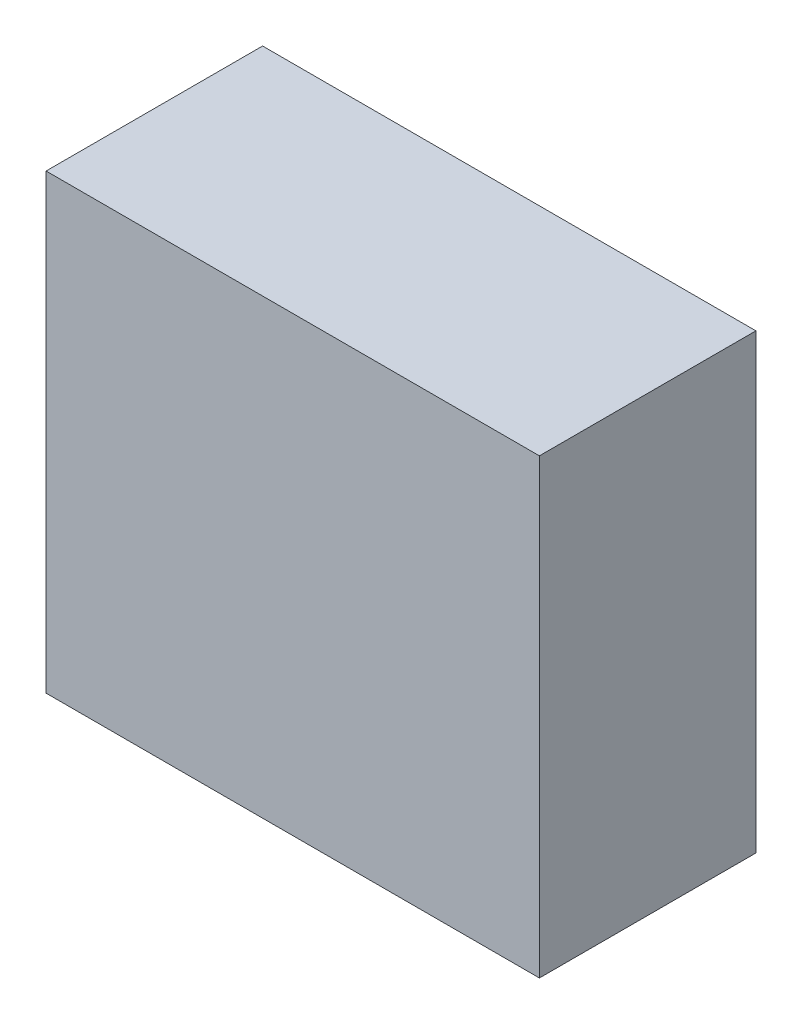
SolidWorks part; units mm, degrees
material "6063-T6, Vareta (SS)"
ref_plane "Plano frontal" through (0, 0, 0) normal (0, 0, 1) x (1, 0, 0)
ref_plane "Plano superior" through (0, 0, 0) normal (0, 1, 0) x (1, 0, 0)
ref_plane "Plano direito" through (0, 0, 0) normal (1, 0, 0) x (0, 0, -1)
sketch "Esboço1" plane through (0, 0, 0) normal (0, 0, 1) x (1, 0, 0)
  line L1 (-18, -16.5) -> (18, -16.5)
  line L2 (-18, -16.5) -> (-18, 16.5)
  line L3 (-18, 16.5) -> (18, 16.5)
  line L4 (18, -16.5) -> (18, 16.5)
  line L5 (-18, -16.5) -> (18, 16.5) construction
  line L6 (-18, 16.5) -> (18, -16.5) construction
  point P0 (0, 0)
  dimension "D1" = 36
  dimension "D2" = 33
extrude "Ressalto-extrusão1" add sketch "Esboço1" along normal blind 15.8
